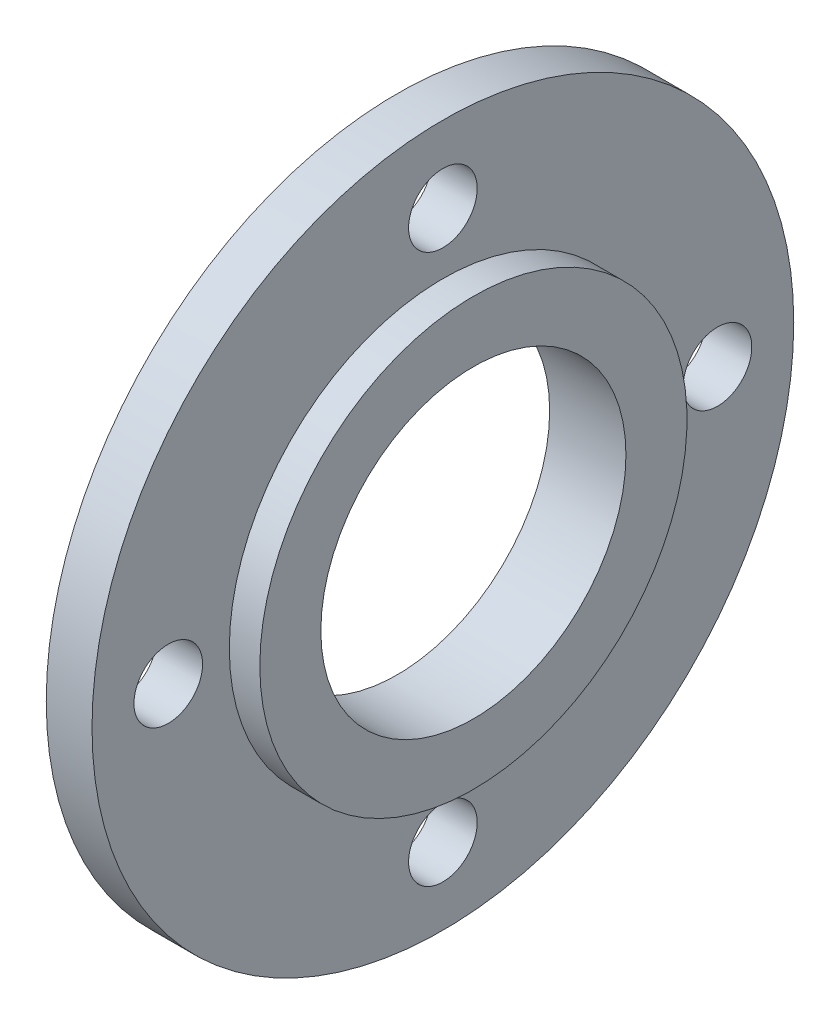
SolidWorks part; units mm, degrees
material "6061 Alloy"
ref_plane "Ön Düzlem" through (0, 0, 0) normal (0, 0, 1) x (1, 0, 0)
ref_plane "Üst Düzlem" through (0, 0, 0) normal (0, 1, 0) x (1, 0, 0)
ref_plane "Sağ Düzlem" through (0, 0, 0) normal (1, 0, 0) x (0, 0, -1)
sketch "Sketch1" plane through (0, 0, 0) normal (0, 0, 1) x (1, 0, 0)
  line L0 (0, 10) -> (5, 10)
  line L1 (5, 10) -> (5, 14)
  line L2 (5, 14) -> (3, 14)
  line L3 (3, 14) -> (3, 23)
  line L4 (3, 23) -> (0, 23)
  line L5 (0, 23) -> (0, 10)
  line L6 (0, 10) -> (0, 0) construction
  line L7 (0, 0) -> (7.3047, 0) construction
  dimension "D1" = 2
  dimension "D2" = 3
  dimension "D3" = 4
  dimension "D4" = 14
  dimension "D5" = 23
revolve "Revolve1" add sketch "Sketch1" angle 360 about L7
sketch "Sketch3" plane through (0, 0, 0) normal (-1, 0, 0) x (0, 0, 1)
  line L0 (0, 0) -> (0, 18) construction
  dimension "D1" = 18
hole_wizard "M4 Clearance Hole1" positions "Sketch4" profile "Sketch6" hole size "M4" standard "ISO" end condition up to next
sketch "Sketch4" plane through (0, 0, 0) normal (-1, 0, 0) x (0, 0, 1)
  point P0 (0, 18)
sketch "Sketch6" plane through (0, 18, 0) normal (0, 1, 0) x (0, 0, 1)
  line L0 (0, 0) -> (0, 3)
  line L1 (0, 3) -> (2.25, 3)
  line L2 (2.25, 3) -> (2.25, 0)
  line L5 (2.25, 0) -> (0, 0)
  line L11 (0, -6.35) -> (0, 107.95) construction
  dimension "Thru Hole Dia." = 4.5
  dimension "Thru Hole Depth" = 3
pattern_circular "CirPattern1" count 4 over 360 about axis through (0, 0, 0) along (1, 0, 0) of "M4 Clearance Hole1"
